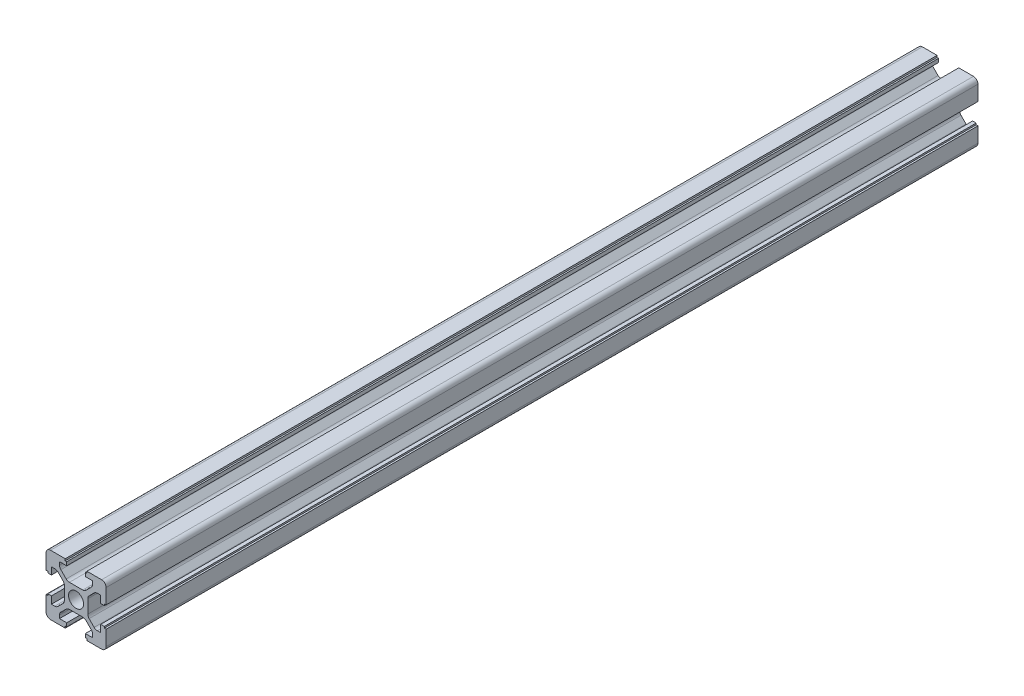
SolidWorks part; units mm, degrees
ref_plane "Front Plane" through (0, 0, 0) normal (0, 0, 1) x (1, 0, 0)
ref_plane "Top Plane" through (0, 0, 0) normal (0, 1, 0) x (1, 0, 0)
ref_plane "Right Plane" through (0, 0, 0) normal (1, 0, 0) x (0, 0, -1)
sketch "Sketch1" plane through (0, 0, 0) normal (0, 0, 1) x (1, 0, 0)
  line L0 (-3.6, -10) -> (-8.5, -10)
  line L1 (-10, -8.5) -> (-10, -3.5)
  line L2 (0, 0) -> (-10, -10) construction
  line L3 (0, 0) -> (0, 11.6126) construction
  line L4 (0, 0) -> (11.7731, -11.7731) construction
  line L5 (8.5, -10) -> (3.6, -10)
  line L6 (10, -8.5) -> (10, -3.5)
  line L7 (3.6, -10) -> (3.6, -9.4)
  line L8 (3.6, -9.4) -> (3.1, -9.4)
  line L9 (3.1, -9.4) -> (3.1, -8.2)
  line L10 (-3.6, -10) -> (-3.6, -9.4)
  line L11 (-3.6, -9.4) -> (-3.1, -9.4)
  line L12 (-3.1, -9.4) -> (-3.1, -8.2)
  line L13 (3.1, -8.2) -> (5.5, -8.2)
  line L14 (-3.1, -8.2) -> (-5.5, -8.2)
  line L15 (-5.5, -8.2) -> (-5.5, -7.182)
  line L16 (-5.0607, -6.1213) -> (-3.2787, -4.3393)
  line L17 (5.5, -8.2) -> (5.5, -7.182)
  line L18 (5.0607, -6.1213) -> (3.2787, -4.3393)
  line L19 (-2.218, -3.9) -> (2.218, -3.9)
  line L20 (-10, -3.5) -> (-9.4, -3.5)
  line L21 (-9.4, -3.5) -> (-9.4, -3)
  line L22 (-9.4, -3) -> (-8.2, -3)
  line L23 (-8.2, -3) -> (-8.2, -5.4)
  line L24 (-8.2, -5.4) -> (-7.082, -5.4)
  line L25 (-6.0213, -4.9607) -> (-4.3393, -3.2787)
  line L26 (-3.9, -2.218) -> (-3.9, 2.218)
  line L27 (10, -3.5) -> (9.4, -3.5)
  line L28 (9.4, -3.5) -> (9.4, -3)
  line L29 (9.4, -3) -> (8.2, -3)
  line L30 (8.2, -3) -> (8.2, -5.4)
  line L31 (8.2, -5.4) -> (7.082, -5.4)
  line L32 (6.0213, -4.9607) -> (4.3393, -3.2787)
  line L33 (3.9, -2.218) -> (3.9, 2.218)
  line L34 (0, 0) -> (-21.3742, 0) construction
  line L35 (6.0213, 4.9607) -> (4.3393, 3.2787)
  line L36 (8.2, 5.4) -> (7.082, 5.4)
  line L37 (8.2, 3) -> (8.2, 5.4)
  line L38 (9.4, 3) -> (8.2, 3)
  line L39 (9.4, 3.5) -> (9.4, 3)
  line L40 (10, 3.5) -> (9.4, 3.5)
  line L41 (10, 8.5) -> (10, 3.5)
  line L42 (8.5, 10) -> (3.6, 10)
  line L43 (3.6, 10) -> (3.6, 9.4)
  line L44 (3.6, 9.4) -> (3.1, 9.4)
  line L45 (3.1, 9.4) -> (3.1, 8.2)
  line L46 (3.1, 8.2) -> (5.5, 8.2)
  line L47 (5.5, 8.2) -> (5.5, 7.182)
  line L48 (5.0607, 6.1213) -> (3.2787, 4.3393)
  line L49 (-2.218, 3.9) -> (2.218, 3.9)
  line L50 (-5.0607, 6.1213) -> (-3.2787, 4.3393)
  line L51 (-5.5, 8.2) -> (-5.5, 7.182)
  line L52 (-3.1, 8.2) -> (-5.5, 8.2)
  line L53 (-3.6, 9.4) -> (-3.1, 9.4)
  line L54 (-3.1, 9.4) -> (-3.1, 8.2)
  line L55 (-3.6, 10) -> (-3.6, 9.4)
  line L56 (-3.6, 10) -> (-8.5, 10)
  line L57 (-10, 8.5) -> (-10, 3.5)
  line L58 (-10, 3.5) -> (-9.4, 3.5)
  line L59 (-9.4, 3.5) -> (-9.4, 3)
  line L60 (-9.4, 3) -> (-8.2, 3)
  line L61 (-8.2, 3) -> (-8.2, 5.4)
  line L62 (-8.2, 5.4) -> (-7.082, 5.4)
  line L63 (-6.0213, 4.9607) -> (-4.3393, 3.2787)
  circle A0 centre (0, 0) radius 2.5
  arc A1 (-10, -8.5) -> (-8.5, -10) centre (-8.5, -8.5) ccw
  arc A2 (10, -8.5) -> (8.5, -10) centre (8.5, -8.5) cw
  arc A3 (10, 8.5) -> (8.5, 10) centre (8.5, 8.5) ccw
  arc A4 (-10, 8.5) -> (-8.5, 10) centre (-8.5, 8.5) cw
  arc A5 (-7.082, -5.4) -> (-6.0213, -4.9607) centre (-7.082, -3.9) ccw
  arc A6 (-7.082, 5.4) -> (-6.0213, 4.9607) centre (-7.082, 3.9) cw
  arc A7 (-5.0607, 6.1213) -> (-5.5, 7.182) centre (-4, 7.182) cw
  arc A8 (5.5, 7.182) -> (5.0607, 6.1213) centre (4, 7.182) cw
  arc A9 (6.0213, 4.9607) -> (7.082, 5.4) centre (7.082, 3.9) cw
  arc A10 (7.082, -5.4) -> (6.0213, -4.9607) centre (7.082, -3.9) cw
  arc A11 (-5.5, -7.182) -> (-5.0607, -6.1213) centre (-4, -7.182) cw
  arc A12 (5.5, -7.182) -> (5.0607, -6.1213) centre (4, -7.182) ccw
  arc A13 (-4.3393, 3.2787) -> (-3.9, 2.218) centre (-5.4, 2.218) cw
  arc A14 (-4.3393, -3.2787) -> (-3.9, -2.218) centre (-5.4, -2.218) ccw
  arc A15 (-3.2787, -4.3393) -> (-2.218, -3.9) centre (-2.218, -5.4) cw
  arc A16 (3.2787, -4.3393) -> (2.218, -3.9) centre (2.218, -5.4) ccw
  arc A17 (4.3393, -3.2787) -> (3.9, -2.218) centre (5.4, -2.218) cw
  arc A18 (4.3393, 3.2787) -> (3.9, 2.218) centre (5.4, 2.218) ccw
  arc A19 (3.2787, 4.3393) -> (2.218, 3.9) centre (2.218, 5.4) cw
  arc A20 (-2.218, 3.9) -> (-3.2787, 4.3393) centre (-2.218, 5.4) cw
  point P16 (10, -10)
  point P17 (4.1697, -5.2303)
  point P45 (3.9, 0)
  point P79 (-3.9, 0)
  point P81 (-6.4607, -5.4)
  point P84 (-6.4607, 5.4)
  point P87 (-5.5, 6.5607)
  point P90 (5.5, 6.5607)
  point P93 (6.4607, 5.4)
  point P96 (6.4607, -5.4)
  point P99 (-5.5, -6.5607)
  point P102 (5.5, -6.5607)
  point P105 (-3.9, 2.8393)
  point P108 (-3.9, -2.8393)
  point P111 (-2.8393, -3.9)
  point P114 (2.8393, -3.9)
  point P117 (3.9, -2.8393)
  point P120 (3.9, 2.8393)
  point P123 (2.8393, 3.9)
  point P126 (-2.8393, 3.9)
  dimension "D1" = 5
  dimension "D5" = 1.5
  dimension "D33" = 1.5
  dimension "D2" = 135
  dimension "D3" = 90
  dimension "D4" = 20
  dimension "D6" = 3.6
  dimension "D7" = 3.6
  dimension "D8" = 0.6
  dimension "D9" = 0.6
  dimension "D10" = 6.2
  dimension "D11" = 3.1
  dimension "D12" = 1.2
  dimension "D13" = 1.2
  dimension "D14" = 11
  dimension "D15" = 5.5
  dimension "D16" = 0.75
  dimension "D17" = 0.75
  dimension "D18" = 6.1
  dimension "D19" = 5
  dimension "D20" = 5
  dimension "D21" = 0.6
  dimension "D22" = 0.5
  dimension "D23" = 1.2
  dimension "D24" = 2.4
  dimension "D25" = 6.1
  dimension "D26" = 1.5
  dimension "D27" = 0.6
  dimension "D28" = 0.5
  dimension "D29" = 1.2
  dimension "D30" = 1.5
  dimension "D31" = 2.4
  dimension "D32" = 6.1
extrude "Boss-Extrude1" add sketch "Sketch1" along normal blind 290
